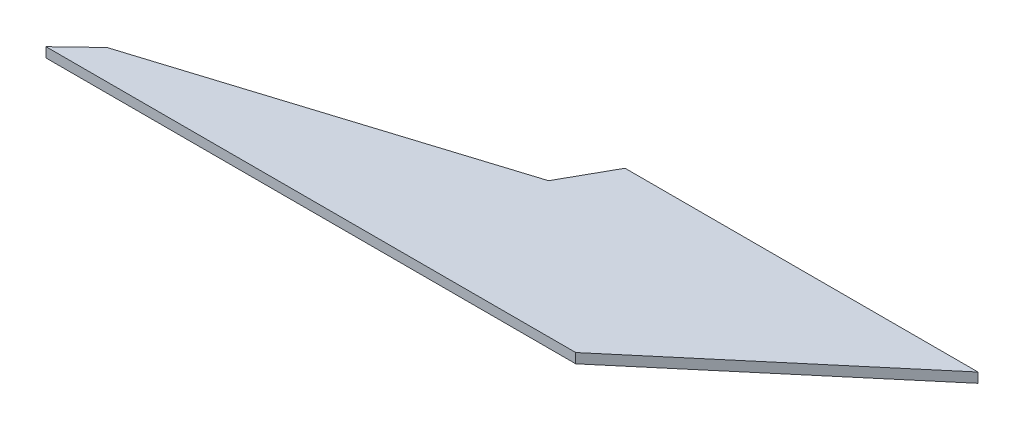
SolidWorks part; units mm, degrees
ref_plane "Plan de face" through (0, 0, 0) normal (0, 0, 1) x (1, 0, 0)
ref_plane "Plan de dessus" through (0, 0, 0) normal (0, 1, 0) x (1, 0, 0)
ref_plane "Plan de droite" through (0, 0, 0) normal (1, 0, 0) x (0, 0, -1)
sketch "Esquisse1" plane through (0, 0, 0) normal (0, 1, 0) x (1, 0, 0)
  line L0 (152.5595, 37.5903) -> (80.5473, 37.5903)
  line L1 (80.5473, 37.5903) -> (74.9513, 27.5851)
  line L2 (74.9513, 27.5851) -> (6.3668, 6.0753)
  line L3 (6.3668, 6.0753) -> (0, 0)
  line L4 (0, 0) -> (108.0784, 0)
  line L5 (108.0784, 0) -> (152.5595, 37.5903)
  point P6 (0, 0)
  point P7 (152.5465, 37.5805)
  point P8 (152.4286, 37.4667)
  point P10 (152.5578, 37.5889)
  point P11 (0, 0)
  point P13 (0, 0)
extrude "Boss.-Extru.1" add sketch "Esquisse1" along normal blind 2
